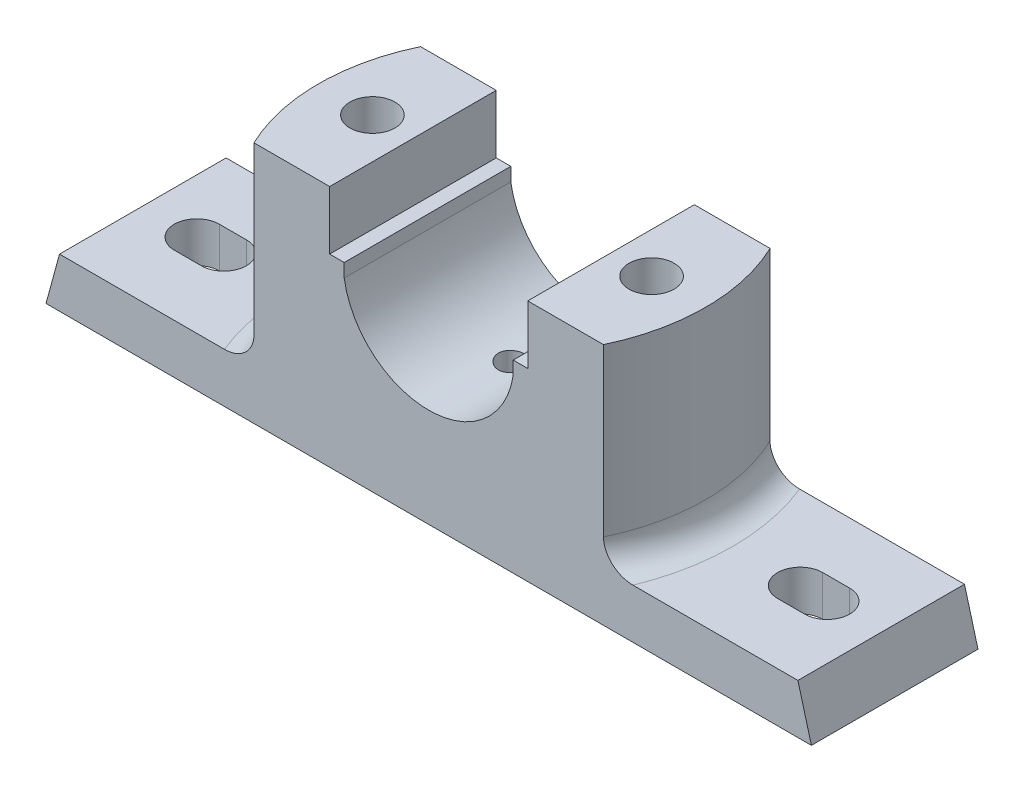
SolidWorks part; units mm, degrees
ref_plane "Front Plane" through (0, 0, 0) normal (0, 0, 1) x (1, 0, 0)
ref_plane "Top Plane" through (0, 0, 0) normal (0, 1, 0) x (1, 0, 0)
ref_plane "Right Plane" through (0, 0, 0) normal (1, 0, 0) x (0, 0, -1)
sketch "Sketch1" plane through (0, 0, 0) normal (0, 0, 1) x (1, 0, 0)
  line L0 (-85, 0) -> (85, 0)
  line L1 (-85, 0) -> (-82, 11)
  line L2 (0, 0) -> (0, 29.629) construction
  line L3 (85, 0) -> (82, 11)
  line L4 (-82, 11) -> (82, 11)
  dimension "D1" = 170
  dimension "D2" = 11
  dimension "D3" = 3
extrude "Boss-Extrude1" add sketch "Sketch1" along normal mid plane 37
sketch "Sketch2" plane through (0, 11, 0) normal (0, 1, 0) x (1, 0, 0)
  line L0 (82, -18.5) -> (-82, -18.5) construction
  line L1 (82, 18.5) -> (-82, 18.5) construction
  line L2 (38.8169, -18.5) -> (-38.8169, -18.5)
  line L3 (38.8169, 18.5) -> (-38.8169, 18.5)
  arc A0 (-38.8169, 18.5) -> (-38.8169, -18.5) centre (0, 0) ccw
  arc A1 (38.8169, -18.5) -> (38.8169, 18.5) centre (0, 0) ccw
extrude "Boss-Extrude2" add sketch "Sketch2" along normal blind 54 from surface at -11 starting at face at (0, 0, 0)
sketch "Sketch3" plane through (0, 0, 0) normal (0, 0, 1) x (1, 0, 0)
  line L0 (0, 0) -> (0, 43.9413) construction
  line L1 (-22, 54) -> (-22, 41)
  line L2 (-38.8169, 54) -> (38.8169, 54) construction
  line L3 (-22, 41) -> (-18.7663, 41)
  line L4 (-18.7663, 41) -> (-18.7663, 38)
  line L5 (18.7663, 41) -> (18.7663, 38)
  line L6 (22, 41) -> (18.7663, 41)
  line L7 (22, 54) -> (22, 41)
  line L8 (-22, 54) -> (22, 54)
  arc A0 (-18.7663, 38) -> (18.7663, 38) centre (0, 40.9706) ccw
  point P11 (0, 21.9706)
  dimension "D1" = 44
  dimension "D4" = 19
  dimension "D2" = 13
  dimension "D3" = 3
extrude "Cut-Extrude1" cut sketch "Sketch3" against normal mid plane 54 contours L8 L7 L6 L5 A0 L4 L3 L1
sketch "Sketch4" plane through (0, 54, 0) normal (0, 1, 0) x (1, 0, 0)
  line L0 (0, 0) -> (0, 47.4347) construction
  circle A0 centre (-31, 0) radius 5
  circle A1 centre (31, 0) radius 5
extrude "Cut-Extrude2" cut sketch "Sketch4" against normal through all
sketch "Sketch5" plane through (0, 0, 0) normal (0, -1, 0) x (1, 0, 0)
  line L0 (0, 0) -> (0, 25.677) construction
  line L1 (-41, 10) -> (-21, 10)
  line L2 (-41, 10) -> (-41, -10)
  line L3 (-41, -10) -> (-21, -10)
  line L4 (-21, 10) -> (-21, -10)
  line L5 (-41, 10) -> (-21, -10) construction
  line L6 (-41, -10) -> (-21, 10) construction
  line L7 (41, -10) -> (21, 10) construction
  line L8 (41, 10) -> (21, -10) construction
  line L9 (21, 10) -> (21, -10)
  line L10 (41, -10) -> (21, -10)
  line L11 (41, 10) -> (41, -10)
  line L12 (41, 10) -> (21, 10)
  point P0 (-31, 0)
  point P13 (31, 0)
  dimension "D1" = 20
extrude "Cut-Extrude3" cut sketch "Sketch5" against normal blind 8
sketch "Sketch6" plane through (0, 0, 0) normal (0, 0, 1) x (1, 0, 0)
  line L0 (-75, 0) -> (-4, 0)
  line L1 (-85, 0) -> (85, 0) construction
  line L2 (-4, 0) -> (-4, 2)
  line L3 (-4, 2) -> (-75, 2)
  line L4 (-75, 2) -> (-75, 0)
  line L5 (0, 0) -> (0, 45.3922) construction
  line L6 (4, 0) -> (4, 2)
  line L7 (75, 0) -> (4, 0)
  line L8 (4, 2) -> (75, 2)
  line L9 (75, 2) -> (75, 0)
  line L10 (0, 45.3922) -> (-67, 45.3922) construction
  line L11 (-67, 45.3922) -> (-67, 8.5018) construction
  line L12 (-75, 8.5018) -> (-59, 8.5018) construction
  dimension "D1" = 10
  dimension "D2" = 4
  dimension "D3" = 2
  dimension "D4" = 2
  dimension "D5" = 67
  dimension "D6" = 16
extrude "Cut-Extrude4" cut sketch "Sketch6" against normal mid plane 22 contours L4 L0 L2 L3
mirror "Mirror1" about plane through (0, 0, 0) normal (1, 0, 0) of "Cut-Extrude4"
sketch "Sketch7" plane through (0, 11, 0) normal (0, 1, 0) x (1, 0, 0)
  line L0 (-64, 0) -> (-70, 0) construction
  line L1 (-64, -5) -> (-70, -5)
  line L2 (-64, 5) -> (-70, 5)
  line L3 (-59, 0) -> (-75, 0) construction
  line L4 (0, 0) -> (0, 32.2372) construction
  line L5 (59, 0) -> (75, 0) construction
  line L6 (64, 0) -> (70, 0) construction
  line L7 (64, -5) -> (70, -5)
  line L8 (64, 5) -> (70, 5)
  arc A0 (-64, -5) -> (-64, 5) centre (-64, 0) ccw
  arc A1 (-70, 5) -> (-70, -5) centre (-70, 0) ccw
  arc A2 (64, -5) -> (64, 5) centre (64, 0) cw
  arc A3 (70, 5) -> (70, -5) centre (70, 0) cw
  point P3 (-67, 0)
  point P16 (67, 0)
  dimension "D1" = 67
  dimension "D2" = 16
  dimension "D3" = 10
extrude "Cut-Extrude5" cut sketch "Sketch7" against normal through all
sketch "Sketch8" plane through (0, 0, 0) normal (0, 0, 1) x (1, 0, 0)
  line L0 (0, 21.9706) -> (0, 14.1681)
  line L1 (0, 14.1681) -> (3, 15.9706)
  line L4 (3, 15.9706) -> (3, 25.4762)
  line L5 (3, 25.4762) -> (0, 25.4762)
  line L6 (0, 25.4762) -> (0, 21.9706)
  arc A0 (-18.7663, 38) -> (18.7663, 38) centre (0, 40.9706) ccw construction
  dimension "D1" = 6
  dimension "D2" = 59
  dimension "D3" = 3
revolve "Cut-Revolve1" cut sketch "Sketch8" angle 360 about L0
fillet "Fillet1" radius 6 2 edges at (43, 11, 0) (-43, 11, 0)
